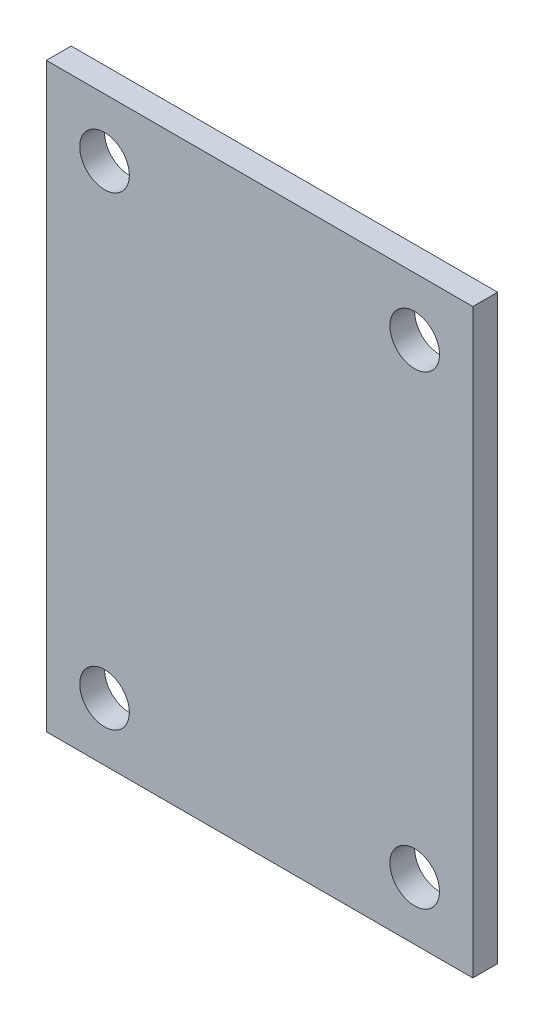
SolidWorks part; units mm, degrees
ref_plane "Спереди" through (0, 0, 0) normal (0, 0, 1) x (1, 0, 0)
ref_plane "Сверху" through (0, 0, 0) normal (0, 1, 0) x (1, 0, 0)
ref_plane "Справа" through (0, 0, 0) normal (1, 0, 0) x (0, 0, -1)
sketch "Эскиз1" plane through (0, 0, 0) normal (0, 0, 1) x (1, 0, 0)
  line L0 (-10, -15) -> (10, 15) construction
  line L1 (-13.75, -18.75) -> (13.75, -18.75)
  line L2 (-13.75, -18.75) -> (-13.75, 18.75)
  line L3 (-13.75, 18.75) -> (13.75, 18.75)
  line L4 (13.75, -18.75) -> (13.75, 18.75)
  line L5 (-13.75, -18.75) -> (13.75, 18.75) construction
  line L6 (-13.75, 18.75) -> (13.75, -18.75) construction
  line L7 (-10, 15) -> (10, -15) construction
  circle A0 centre (-10, 15) radius 1.6
  circle A1 centre (10, 15) radius 1.6
  circle A2 centre (10, -15) radius 1.6
  circle A3 centre (-10, -15) radius 1.6
  point P0 (0, 0)
  dimension "D3" = 20
  dimension "D4" = 30
  dimension "D5" = 3.2
  dimension "D1" = 27.5
  dimension "D2" = 37.5
extrude "Бобышка-Вытянуть1" add sketch "Эскиз1" along normal blind 1.6
